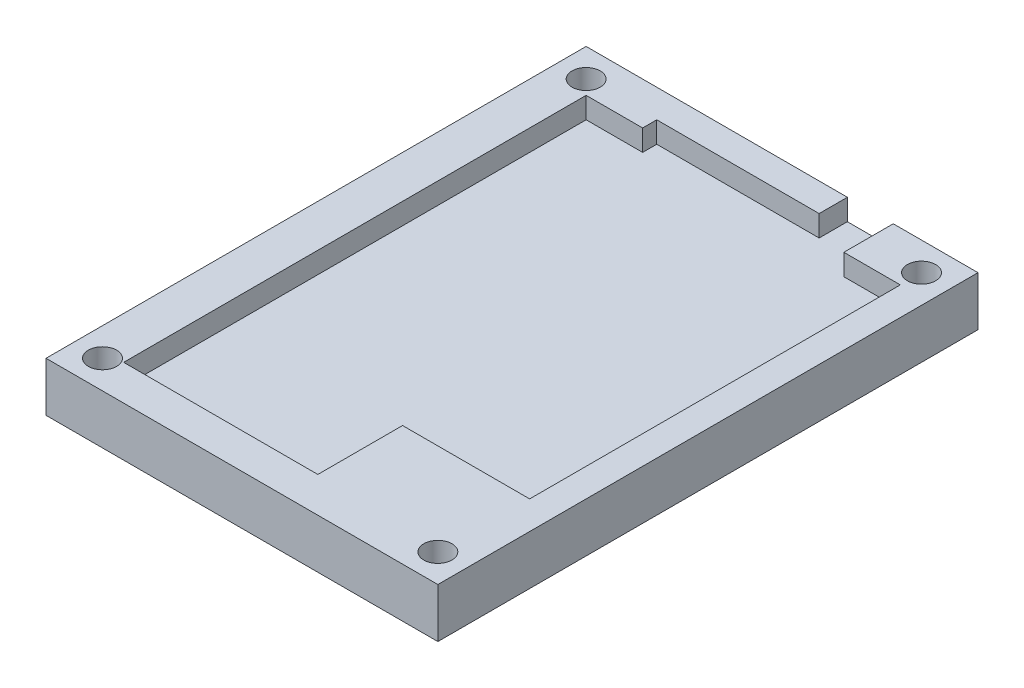
SolidWorks part; units mm, degrees
ref_plane "Front Plane" through (0, 0, 0) normal (0, 0, 1) x (1, 0, 0)
ref_plane "Top Plane" through (0, 0, 0) normal (0, 1, 0) x (1, 0, 0)
ref_plane "Right Plane" through (0, 0, 0) normal (1, 0, 0) x (0, 0, -1)
sketch "Sketch1" plane through (0, 0, 0) normal (0, 1, 0) x (1, 0, 0)
  line L1 (-21.4896, 26.2694) -> (34.0104, 26.2694)
  line L2 (-21.4896, 26.2694) -> (-21.4896, -50.2306)
  line L3 (-21.4896, -50.2306) -> (34.0104, -50.2306)
  line L4 (34.0104, 26.2694) -> (34.0104, -50.2306)
  dimension "D1" = 55.5
  dimension "D2" = 76.5
extrude "Boss-Extrude1" add sketch "Sketch1" along normal blind 4
sketch "Sketch2" plane through (0, 4, 0) normal (0, 1, 0) x (1, 0, 0)
  line L2 (-21.4896, 26.2694) -> (-21.4896, -50.2306)
  line L4 (-15.4896, 20.2694) -> (-15.4896, -45.2306)
  line L8 (-7.4896, 22.2694) -> (15.5104, 22.2694)
  line L9 (15.5104, 26.2694) -> (15.5104, 22.2694)
  line L12 (-15.4896, 20.2694) -> (-7.4896, 20.2694)
  line L13 (-7.4896, 22.2694) -> (-7.4896, 20.2694)
  line L16 (-15.4896, -45.2306) -> (12.0104, -45.2306)
  line L22 (30.0104, -33.2306) -> (30.0104, 19.2694)
  line L26 (30.0104, -33.2306) -> (12.0104, -33.2306)
  line L27 (12.0104, -45.2306) -> (12.0104, -33.2306)
  line L28 (34.0104, 26.2694) -> (34.0104, -50.2306)
  line L29 (34.0104, 26.2694) -> (22.0104, 26.2694)
  line L31 (30.0104, 19.2694) -> (22.0104, 19.2694)
  line L32 (22.0104, 26.2694) -> (22.0104, 19.2694)
  line L33 (-21.4896, -50.2306) -> (34.0104, -50.2306)
  line L34 (-21.4896, 26.2694) -> (15.5104, 26.2694)
  dimension "D1" = 6
  dimension "D5" = 12
  dimension "D6" = 18
  dimension "D7" = 7
extrude "Boss-Extrude2" add sketch "Sketch2" along normal blind 3
hole_wizard "Ø4.0 (4) Diameter Hole1" positions "Sketch3" profile "Sketch5" hole size "Ø4.0" standard "DIN" end condition up to next
sketch "Sketch3" plane through (0, 7, 0) normal (0, 1, 0) x (1, 0, 0)
  line L0 (15.5104, 26.2694) -> (-21.4896, 26.2694) construction
  line L1 (-21.4896, 26.2694) -> (-21.4896, -50.2306) construction
  line L2 (-21.4896, -50.2306) -> (34.0104, -50.2306) construction
  line L3 (34.0104, -50.2306) -> (34.0104, 26.2694) construction
  line L4 (34.0104, 26.2694) -> (22.0104, 26.2694) construction
  point P0 (30.0104, 22.2694)
  point P2 (30.0104, -46.2306)
  point P4 (-17.4896, -46.2306)
  point P6 (-17.4896, 22.2694)
  dimension "D1" = 4
  dimension "D2" = 4
  dimension "D3" = 4
  dimension "D4" = 4
  dimension "D5" = 4
  dimension "D6" = 4
  dimension "D7" = 4
  dimension "D8" = 4
sketch "Sketch5" plane through (30.0104, 7, -22.2694) normal (1, 0, 0) x (0, 0, 1)
  line L0 (0, 0) -> (0, 7)
  line L1 (0, 7) -> (2, 7)
  line L2 (2, 7) -> (2, 0)
  line L5 (2, 0) -> (0, 0)
  line L11 (0, -6.35) -> (0, 107.95) construction
  dimension "Thru Hole Dia." = 4
  dimension "Thru Hole Depth" = 7
